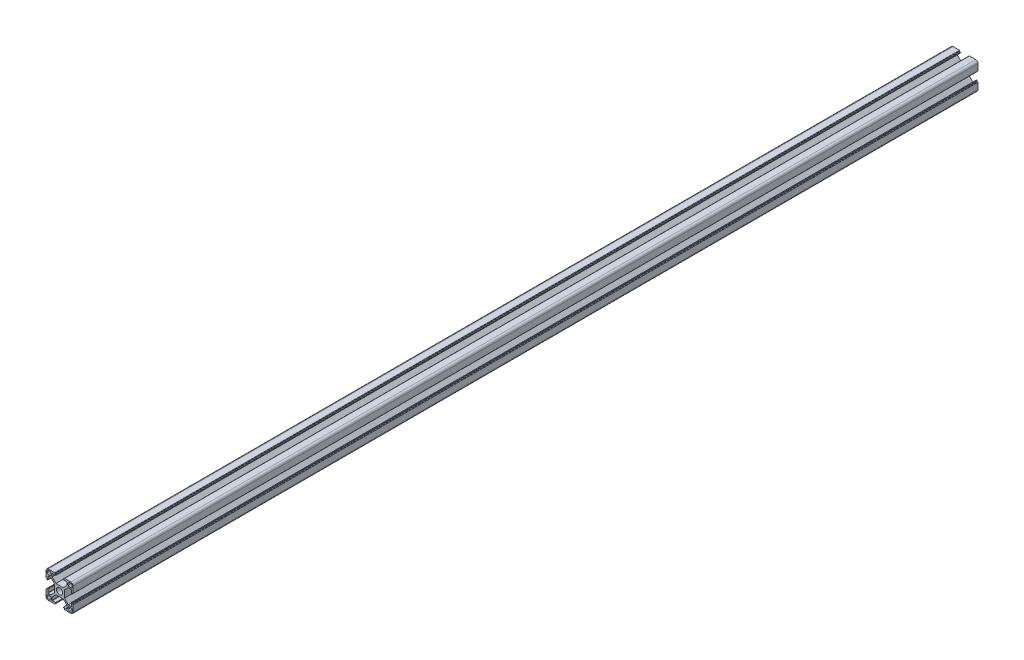
SolidWorks part; units mm, degrees
material "6063 T5"
ref_plane "Спереди" through (0, 0, 0) normal (0, 0, 1) x (1, 0, 0)
ref_plane "Сверху" through (0, 0, 0) normal (0, 1, 0) x (1, 0, 0)
ref_plane "Справа" through (0, 0, 0) normal (1, 0, 0) x (0, 0, -1)
sketch "Эскиз1" plane through (0, 0, 0) normal (0, 0, 1) x (1, 0, 0)
  line L0 (-15.0102, 15.2893) -> (14.9898, 15.2893) construction
  line L1 (-15, -8.25) -> (-15, -12.5)
  line L2 (-12.45, -9.55) -> (-10.85, -9.55)
  line L3 (-13.75, -10.85) -> (-13.75, -12.45)
  line L4 (-12.45, -13.75) -> (-10.85, -13.75)
  line L5 (-9.55, -10.85) -> (-9.55, -12.45)
  line L6 (-12.5, -15) -> (-8.25, -15)
  line L7 (-8.25, 15) -> (-12.5, 15)
  line L8 (-9.55, 12.45) -> (-9.55, 10.85)
  line L9 (-10.85, 13.75) -> (-12.45, 13.75)
  line L10 (-13.75, 12.45) -> (-13.75, 10.85)
  line L11 (-10.85, 9.55) -> (-12.45, 9.55)
  line L12 (-15, 12.5) -> (-15, 8.25)
  line L13 (15, 8.25) -> (15, 12.5)
  line L14 (12.45, 9.55) -> (10.85, 9.55)
  line L15 (13.75, 10.85) -> (13.75, 12.45)
  line L16 (12.45, 13.75) -> (10.85, 13.75)
  line L17 (9.55, 10.85) -> (9.55, 12.45)
  line L18 (12.5, 15) -> (8.25, 15)
  line L19 (8.25, -15) -> (12.5, -15)
  line L20 (9.55, -12.45) -> (9.55, -10.85)
  line L21 (10.85, -13.75) -> (12.45, -13.75)
  line L22 (13.75, -12.45) -> (13.75, -10.85)
  line L23 (10.85, -9.55) -> (12.45, -9.55)
  line L24 (15, -12.5) -> (15, -8.25)
  line L25 (0, 0) -> (-9.55, -10.85) construction
  circle A0 centre (0, 0) radius 3.4
  arc A1 (-10.85, -13.75) -> (-9.55, -12.45) centre (-10.85, -12.45) ccw
  arc A2 (-13.75, -12.45) -> (-12.45, -13.75) centre (-12.45, -12.45) ccw
  arc A3 (-10.85, -9.55) -> (-9.55, -10.85) centre (-10.85, -10.85) cw
  arc A4 (-12.45, -9.55) -> (-13.75, -10.85) centre (-12.45, -10.85) ccw
  arc A5 (-15, -12.5) -> (-12.5, -15) centre (-12.5, -12.5) ccw
  arc A6 (-13.75, 10.85) -> (-12.45, 9.55) centre (-12.45, 10.85) ccw
  arc A7 (-12.45, 13.75) -> (-13.75, 12.45) centre (-12.45, 12.45) ccw
  arc A8 (-9.55, 10.85) -> (-10.85, 9.55) centre (-10.85, 10.85) cw
  arc A9 (-9.55, 12.45) -> (-10.85, 13.75) centre (-10.85, 12.45) ccw
  arc A10 (-12.5, 15) -> (-15, 12.5) centre (-12.5, 12.5) ccw
  arc A11 (10.85, 13.75) -> (9.55, 12.45) centre (10.85, 12.45) ccw
  arc A12 (13.75, 12.45) -> (12.45, 13.75) centre (12.45, 12.45) ccw
  arc A13 (10.85, 9.55) -> (9.55, 10.85) centre (10.85, 10.85) cw
  arc A14 (12.45, 9.55) -> (13.75, 10.85) centre (12.45, 10.85) ccw
  arc A15 (15, 12.5) -> (12.5, 15) centre (12.5, 12.5) ccw
  arc A16 (13.75, -10.85) -> (12.45, -9.55) centre (12.45, -10.85) ccw
  arc A17 (12.45, -13.75) -> (13.75, -12.45) centre (12.45, -12.45) ccw
  arc A18 (9.55, -10.85) -> (10.85, -9.55) centre (10.85, -10.85) cw
  arc A19 (9.55, -12.45) -> (10.85, -13.75) centre (10.85, -12.45) ccw
  arc A20 (12.5, -15) -> (15, -12.5) centre (12.5, -12.5) ccw
  point P5 (0, 0)
  point P16 (-13.75, -13.75)
  point P21 (-13.75, -9.55)
  line B0 (-8.25, -15) -> (-5.5, -15)
  line B1 (-5.2, -14.7) -> (-5.2, -14.3)
  line B2 (-4.9, -14) -> (-4.4, -14)
  line B3 (-4.1, -13.7) -> (-4.1, -13.3)
  line B4 (-4.4, -13) -> (-7.95, -13)
  line B5 (-8.25, -12.7) -> (-8.25, -9.65)
  line B6 (-8.25, -9.65) -> (-4, -5.4)
  line B7 (0, -5.4) -> (0, -15) construction
  line B8 (4, -5.4) -> (-4, -5.4)
  line B9 (8.25, -9.65) -> (4, -5.4)
  line B10 (8.25, -12.7) -> (8.25, -9.65)
  line B11 (4.4, -13) -> (7.95, -13)
  line B12 (4.1, -13.7) -> (4.1, -13.3)
  line B13 (4.9, -14) -> (4.4, -14)
  line B14 (5.2, -14.7) -> (5.2, -14.3)
  line B15 (8.25, -15) -> (5.5, -15)
  arc B16 (-7.95, -13) -> (-8.25, -12.7) centre (-7.95, -12.7) cw
  arc B17 (-4.1, -13.3) -> (-4.4, -13) centre (-4.4, -13.3) ccw
  arc B18 (-4.4, -14) -> (-4.1, -13.7) centre (-4.4, -13.7) ccw
  arc B19 (-5.2, -14.3) -> (-4.9, -14) centre (-4.9, -14.3) cw
  arc B20 (-5.5, -15) -> (-5.2, -14.7) centre (-5.5, -14.7) ccw
  arc B21 (5.5, -15) -> (5.2, -14.7) centre (5.5, -14.7) cw
  arc B22 (5.2, -14.3) -> (4.9, -14) centre (4.9, -14.3) ccw
  arc B23 (4.4, -14) -> (4.1, -13.7) centre (4.4, -13.7) cw
  arc B24 (4.1, -13.3) -> (4.4, -13) centre (4.4, -13.3) cw
  arc B25 (7.95, -13) -> (8.25, -12.7) centre (7.95, -12.7) ccw
  line B26 (-15, 8.25) -> (-15, 5.5)
  line B27 (-14.7, 5.2) -> (-14.3, 5.2)
  line B28 (-14, 4.9) -> (-14, 4.4)
  line B29 (-13.7, 4.1) -> (-13.3, 4.1)
  line B30 (-13, 4.4) -> (-13, 7.95)
  line B31 (-12.7, 8.25) -> (-9.65, 8.25)
  line B32 (-9.65, 8.25) -> (-5.4, 4)
  line B33 (-5.4, 0) -> (-15, 0) construction
  line B34 (-5.4, -4) -> (-5.4, 4)
  line B35 (-9.65, -8.25) -> (-5.4, -4)
  line B36 (-12.7, -8.25) -> (-9.65, -8.25)
  line B37 (-13, -4.4) -> (-13, -7.95)
  line B38 (-13.7, -4.1) -> (-13.3, -4.1)
  line B39 (-14, -4.9) -> (-14, -4.4)
  line B40 (-14.7, -5.2) -> (-14.3, -5.2)
  line B41 (-15, -8.25) -> (-15, -5.5)
  arc B42 (-13, 7.95) -> (-12.7, 8.25) centre (-12.7, 7.95) cw
  arc B43 (-13.3, 4.1) -> (-13, 4.4) centre (-13.3, 4.4) ccw
  arc B44 (-14, 4.4) -> (-13.7, 4.1) centre (-13.7, 4.4) ccw
  arc B45 (-14.3, 5.2) -> (-14, 4.9) centre (-14.3, 4.9) cw
  arc B46 (-15, 5.5) -> (-14.7, 5.2) centre (-14.7, 5.5) ccw
  arc B47 (-15, -5.5) -> (-14.7, -5.2) centre (-14.7, -5.5) cw
  arc B48 (-14.3, -5.2) -> (-14, -4.9) centre (-14.3, -4.9) ccw
  arc B49 (-14, -4.4) -> (-13.7, -4.1) centre (-13.7, -4.4) cw
  arc B50 (-13.3, -4.1) -> (-13, -4.4) centre (-13.3, -4.4) cw
  arc B51 (-13, -7.95) -> (-12.7, -8.25) centre (-12.7, -7.95) ccw
  line B52 (8.25, 15) -> (5.5, 15)
  line B53 (5.2, 14.7) -> (5.2, 14.3)
  line B54 (4.9, 14) -> (4.4, 14)
  line B55 (4.1, 13.7) -> (4.1, 13.3)
  line B56 (4.4, 13) -> (7.95, 13)
  line B57 (8.25, 12.7) -> (8.25, 9.65)
  line B58 (8.25, 9.65) -> (4, 5.4)
  line B59 (0, 5.4) -> (0, 15) construction
  line B60 (-4, 5.4) -> (4, 5.4)
  line B61 (-8.25, 9.65) -> (-4, 5.4)
  line B62 (-8.25, 12.7) -> (-8.25, 9.65)
  line B63 (-4.4, 13) -> (-7.95, 13)
  line B64 (-4.1, 13.7) -> (-4.1, 13.3)
  line B65 (-4.9, 14) -> (-4.4, 14)
  line B66 (-5.2, 14.7) -> (-5.2, 14.3)
  line B67 (-8.25, 15) -> (-5.5, 15)
  arc B68 (7.95, 13) -> (8.25, 12.7) centre (7.95, 12.7) cw
  arc B69 (4.1, 13.3) -> (4.4, 13) centre (4.4, 13.3) ccw
  arc B70 (4.4, 14) -> (4.1, 13.7) centre (4.4, 13.7) ccw
  arc B71 (5.2, 14.3) -> (4.9, 14) centre (4.9, 14.3) cw
  arc B72 (5.5, 15) -> (5.2, 14.7) centre (5.5, 14.7) ccw
  arc B73 (-5.5, 15) -> (-5.2, 14.7) centre (-5.5, 14.7) cw
  arc B74 (-5.2, 14.3) -> (-4.9, 14) centre (-4.9, 14.3) ccw
  arc B75 (-4.4, 14) -> (-4.1, 13.7) centre (-4.4, 13.7) cw
  arc B76 (-4.1, 13.3) -> (-4.4, 13) centre (-4.4, 13.3) cw
  arc B77 (-7.95, 13) -> (-8.25, 12.7) centre (-7.95, 12.7) ccw
  line B78 (15, -8.25) -> (15, -5.5)
  line B79 (14.7, -5.2) -> (14.3, -5.2)
  line B80 (14, -4.9) -> (14, -4.4)
  line B81 (13.7, -4.1) -> (13.3, -4.1)
  line B82 (13, -4.4) -> (13, -7.95)
  line B83 (12.7, -8.25) -> (9.65, -8.25)
  line B84 (9.65, -8.25) -> (5.4, -4)
  line B85 (5.4, 0) -> (15, 0) construction
  line B86 (5.4, 4) -> (5.4, -4)
  line B87 (9.65, 8.25) -> (5.4, 4)
  line B88 (12.7, 8.25) -> (9.65, 8.25)
  line B89 (13, 4.4) -> (13, 7.95)
  line B90 (13.7, 4.1) -> (13.3, 4.1)
  line B91 (14, 4.9) -> (14, 4.4)
  line B92 (14.7, 5.2) -> (14.3, 5.2)
  line B93 (15, 8.25) -> (15, 5.5)
  arc B94 (13, -7.95) -> (12.7, -8.25) centre (12.7, -7.95) cw
  arc B95 (13.3, -4.1) -> (13, -4.4) centre (13.3, -4.4) ccw
  arc B96 (14, -4.4) -> (13.7, -4.1) centre (13.7, -4.4) ccw
  arc B97 (14.3, -5.2) -> (14, -4.9) centre (14.3, -4.9) cw
  arc B98 (15, -5.5) -> (14.7, -5.2) centre (14.7, -5.5) ccw
  arc B99 (15, 5.5) -> (14.7, 5.2) centre (14.7, 5.5) cw
  arc B100 (14.3, 5.2) -> (14, 4.9) centre (14.3, 4.9) ccw
  arc B101 (14, 4.4) -> (13.7, 4.1) centre (13.7, 4.4) cw
  arc B102 (13.3, 4.1) -> (13, 4.4) centre (13.3, 4.4) cw
  arc B103 (13, 7.95) -> (12.7, 8.25) centre (12.7, 7.95) ccw
  dimension "D2" = 6.8
  dimension "D6" = 1.3
  dimension "D7" = 2.5
  dimension "D1" = 15
  dimension "D3" = 4.2
  dimension "D4" = 1.3
  dimension "D5" = 1.3
  dimension "D8" = 4
sketch_block_instance "Блок1-2"
sketch_block "Блок1" parameters "D7"=0.3, "D1"=16.5, "D2"=2, "D3"=8, "D4"=9.6, "D5"=45, "D6"=10.4
sketch_block_instance "Блок1-4"
sketch_block_instance "Блок1-5"
sketch_block_instance "Блок1-6"
extrude "Бобышка-Вытянуть1" add sketch "Эскиз1" along normal blind 1000 contours B103 B89 B102 B90 B101 B91 B100 B92 B99 B93 L13 A15 L18 B52 B72 B53 B71 B54 B70 B55 B69 B56 B68 B57 B58 B60 B61 B62 B77 B63 B76 B64 B75 B65 B74 B66 B73 B67 L7 A10 L12 B26 B46 B27 B45 B28 B44 B29 B43 B30 B42
